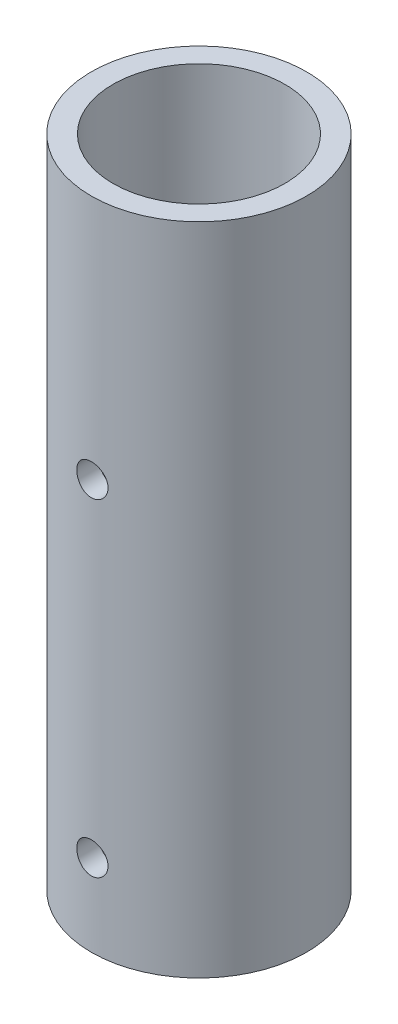
SolidWorks part; units mm, degrees
material "6061-T6 (SS)"
ref_plane "Front Plane" through (0, 0, 0) normal (0, 0, 1) x (1, 0, 0)
ref_plane "Top Plane" through (0, 0, 0) normal (0, 1, 0) x (1, 0, 0)
ref_plane "Right Plane" through (0, 0, 0) normal (1, 0, 0) x (0, 0, -1)
sketch "Sketch1" plane through (0, 0, 0) normal (0, 1, 0) x (1, 0, 0)
  circle A0 centre (0, 0) radius 16.7005
  circle A1 centre (0, 0) radius 13.335
  dimension "D1" = 33.401
  dimension "D2" = 26.67
extrude "Boss-Extrude1" add sketch "Sketch1" along normal blind 101.6
sketch "Sketch2" plane through (0, 0, 0) normal (0, 0, 1) x (1, 0, 0)
  line L0 (16.7005, 101.6) -> (-16.7005, 101.6) construction
  circle A0 centre (0, 63.5) radius 2.4257
  circle A1 centre (0, 12.7) radius 2.4257
  dimension "D2" = 4.8514
  dimension "D3" = 38.1
  dimension "D4" = 50.8
extrude "Cut-Extrude1" cut sketch "Sketch2" against normal through all both and the other way through all
